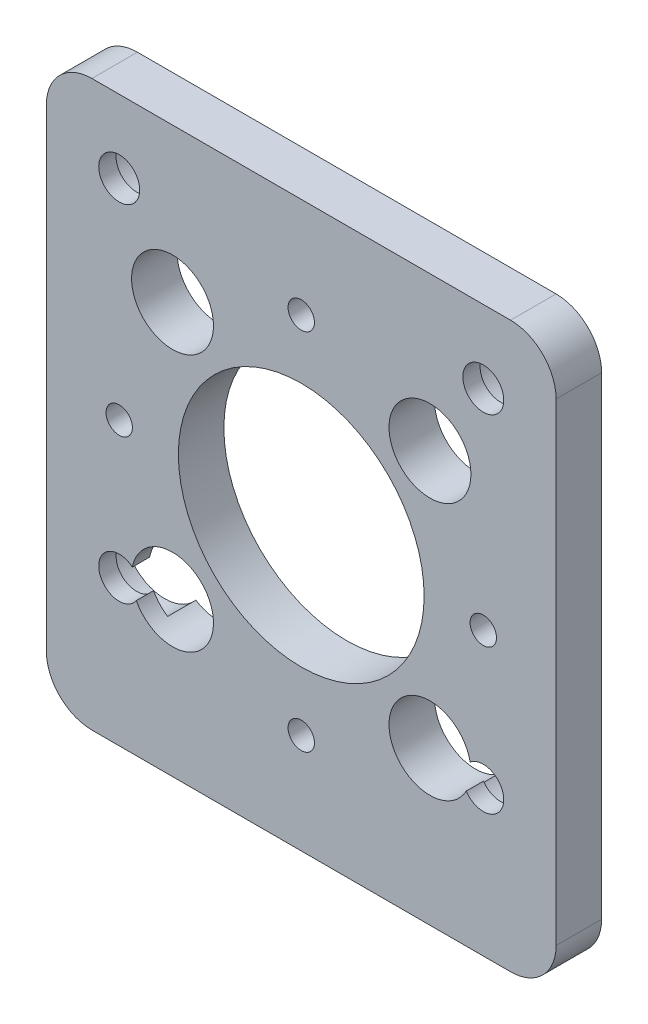
SolidWorks part; units mm, degrees
ref_plane "Front Plane" through (0, 0, 0) normal (0, 0, 1) x (1, 0, 0)
ref_plane "Top Plane" through (0, 0, 0) normal (0, 1, 0) x (1, 0, 0)
ref_plane "Right Plane" through (0, 0, 0) normal (1, 0, 0) x (0, 0, -1)
sketch "Sketch1" plane through (0, 0, 0) normal (0, 0, 1) x (1, 0, 0)
  line L1 (-20, 23) -> (20, 23) construction
  line L2 (-20, 23) -> (-20, -15) construction
  line L3 (-20, -15) -> (20, -15) construction
  line L4 (20, 23) -> (20, -15) construction
  line L5 (-28, -31) -> (28, -31)
  line L6 (-28, -31) -> (-28, 31)
  line L7 (-28, 31) -> (28, 31)
  line L8 (28, -31) -> (28, 31)
  line L9 (-28, -31) -> (28, 31) construction
  line L10 (-28, 31) -> (28, -31) construction
  circle A0 centre (0, 0) radius 20 construction
  circle A1 centre (0, 0) radius 13.5
  dimension "D7" = 40
  dimension "D8" = 27
  dimension "D1" = 15
  dimension "D2" = 23
  dimension "D3" = 20
  dimension "D4" = 20
  dimension "D5" = 8
  dimension "D6" = 8
extrude "Boss-Extrude1" add sketch "Sketch1" along normal blind 5
sketch "Sketch2" plane through (0, 0, 0) normal (0, 0, -1) x (-1, 0, 0)
  circle A0 centre (0, 0) radius 20 construction
  point P0 (0, 20)
  point P4 (0, -20)
  point P7 (20, 0)
  point P9 (-20, 0)
hole_wizard "M2.5 Clearance Hole1" positions "Sketch2" profile "Sketch3" hole size "M2.5" standard "ANSI Metric" end condition through all
sketch "Sketch3" plane through (0, 20, 0) normal (1, 0, 0) x (0, 1, 0)
  line L0 (0, 0) -> (0, 5)
  line L1 (0, 5) -> (1.45, 5)
  line L2 (1.45, 5) -> (1.45, 0)
  line L5 (1.45, 0) -> (0, 0)
  line L11 (0, -6.35) -> (0, 107.95) construction
  dimension "Thru Hole Dia." = 2.9
  dimension "Thru Hole Depth" = 5
sketch "Sketch4" plane through (0, 0, 0) normal (0, 0, -1) x (-1, 0, 0)
  point P0 (-20, 23)
  point P3 (20, 23)
  point P6 (20, -15)
  point P9 (-20, -15)
hole_wizard "CBORE for M4 Pan Head Machine Screw1" positions "Sketch4" profile "Sketch5" counterbore size "M4" standard "ANSI Metric" end condition through all
sketch "Sketch5" plane through (20, 23, 0) normal (1, 0, 0) x (0, 1, 0)
  line L0 (0, 0) -> (0, 5)
  line L1 (0, 5) -> (2.25, 5)
  line L3 (2.25, 5) -> (2.25, 3.1)
  line L4 (2.25, 3.1) -> (4.5, 3.1)
  line L5 (4.5, 3.1) -> (4.5, 0)
  line L7 (4.5, 0) -> (0, 0)
  line L11 (0, -6.35) -> (0, 107.95) construction
  dimension "Thru Hole Dia." = 4.5
  dimension "Thru Hole Depth" = 5
  dimension "C'Bore Dia." = 9
  dimension "C'Bore Depth" = 3.1
fillet "Fillet1" radius 5 4 edges at (28, -31, 2.5) (-28, -31, 2.5) (-28, 31, 2.5) (28, 31, 2.5)
sketch "Sketch6" plane through (0, 0, 0) normal (0, 0, 1) x (1, 0, 0)
  line L0 (-1000, 0) -> (49000, 0) construction
  line L1 (-14.1421, 14.1421) -> (14.1421, -14.1421) construction
  line L2 (-14.1421, -14.1421) -> (14.1421, 14.1421) construction
  circle A0 centre (0, 0) radius 20 construction
  circle A1 centre (-14.1421, -14.1421) radius 4.5
  circle A2 centre (-14.1421, 14.1421) radius 4.5
  circle A3 centre (14.1421, 14.1421) radius 4.5
  circle A4 centre (14.1421, -14.1421) radius 4.5
  point P3 (0, 0)
  point P9 (0, 0)
  dimension "D1" = 40
  dimension "D3" = 9
  dimension "D2" = 45
sketch "Sketch7" plane through (0, 0, 5) normal (0, 0, 1) x (1, 0, 0)
  point P0 (-14.1421, 14.1421)
  point P3 (-14.1421, -14.1421)
  point P6 (14.1421, -14.1421)
  point P9 (14.1421, 14.1421)
hole_wizard "CBORE for M4 Pan Head Machine Screw2" positions "Sketch7" profile "Sketch8" counterbore size "M4" standard "ANSI Metric"
sketch "Sketch8" plane through (-14.1421, 14.1421, 5) normal (1, 0, 0) x (0, -1, 0)
  line L0 (0, 0) -> (0, 5)
  line L1 (0, 5) -> (2.25, 5)
  line L3 (2.25, 5) -> (2.25, 3.1)
  line L4 (2.25, 3.1) -> (4.5, 3.1)
  line L5 (4.5, 3.1) -> (4.5, 0)
  line L7 (4.5, 0) -> (0, 0)
  line L11 (0, -6.35) -> (0, 107.95) construction
  dimension "Thru Hole Dia." = 4.5
  dimension "Thru Hole Depth" = 5
  dimension "C'Bore Dia." = 9
  dimension "C'Bore Depth" = 3.1
extrude "Cut-Extrude1" cut sketch "Sketch6" against normal through all both and the other way through all
